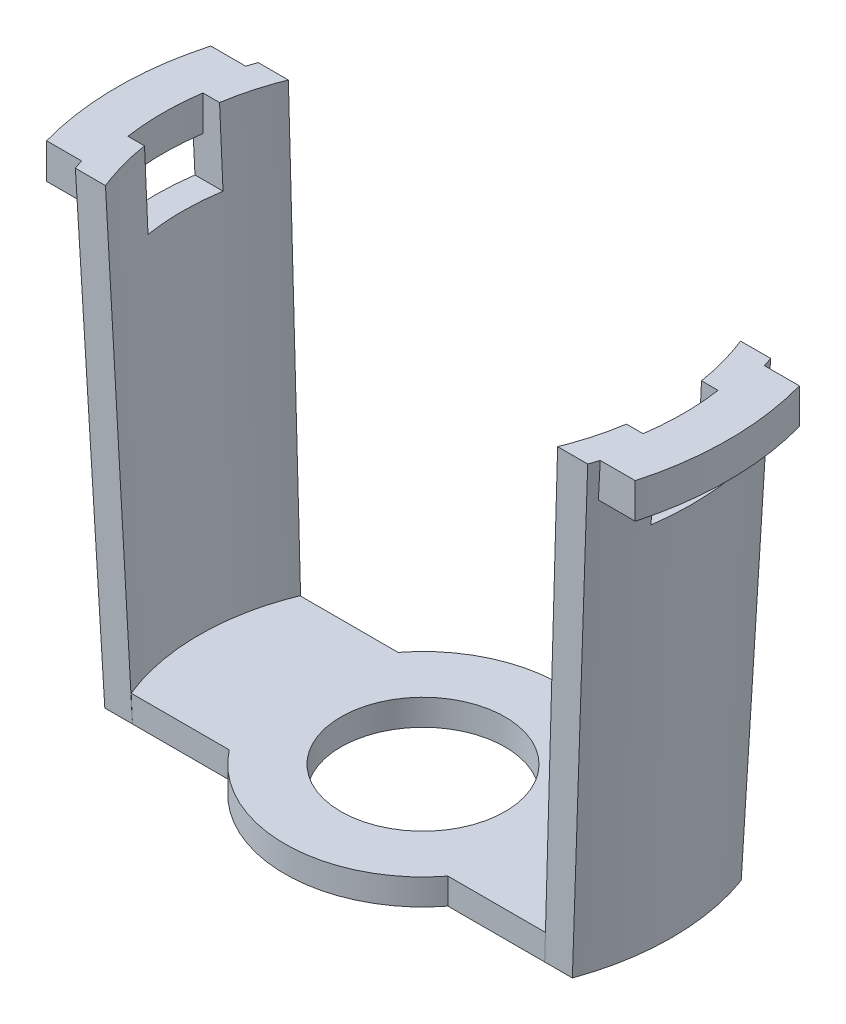
SolidWorks part; units mm, degrees
material "PE Low/Medium Density"
ref_plane "Front Plane" through (0, 0, 0) normal (0, 0, 1) x (1, 0, 0)
ref_plane "Top Plane" through (0, 0, 0) normal (0, 1, 0) x (1, 0, 0)
ref_plane "Right Plane" through (0, 0, 0) normal (1, 0, 0) x (0, 0, -1)
sketch "Sketch1" plane through (0, 0, 0) normal (0, 1, 0) x (1, 0, 0)
  line L0 (-13.462, 0) -> (13.462, 0) construction
  line L1 (-12.6618, 4.572) -> (-5.9204, 4.572)
  line L2 (5.9204, 4.572) -> (12.6618, 4.572)
  line L3 (-12.6618, -4.572) -> (-5.9204, -4.572)
  line L4 (5.9204, -4.572) -> (12.6618, -4.572)
  arc A0 (-5.9204, -4.572) -> (5.9204, -4.572) centre (0, 0) ccw
  circle A1 centre (0, 0) radius 4.445
  arc A2 (-12.6618, 4.572) -> (-12.6618, -4.572) centre (0, 0) ccw
  arc A3 (12.6618, -4.572) -> (12.6618, 4.572) centre (0, 0) ccw
  arc A4 (5.9204, 4.572) -> (-5.9204, 4.572) centre (0, 0) ccw
  dimension "D1" = 7.4803
  dimension "D2" = 8.89
  dimension "D4" = 13.462
  dimension "D5" = 9.144
extrude "Base" add sketch "Sketch1" along normal blind 1.4097
ref_plane "Plane1" through (0, 24.9047, 0) normal (0, -1, 0) x (-1, 0, 0)
sketch "Sketch3" plane through (0, 0, 0) normal (0, 1, 0) x (1, 0, 0)
  line L0 (-12.6618, -4.572) -> (-11.1632, -4.572)
  line L1 (-12.6618, -4.572) -> (-5.9204, -4.572) construction
  line L2 (-12.6618, 4.572) -> (-11.1632, 4.572)
  line L3 (-5.9204, 4.572) -> (-12.6618, 4.572) construction
  arc A0 (-12.6618, -4.572) -> (-12.6618, 4.572) centre (0, 0) cw
  arc A1 (-11.1632, 4.572) -> (-11.1632, -4.572) centre (0, 0) ccw
  arc A2 (-12.6618, 4.572) -> (-12.6618, -4.572) centre (0, 0) ccw construction
  dimension "D2" = 1.4986
sketch "Sketch2" plane through (0, 24.9047, 0) normal (0, -1, 0) x (-1, 0, 0)
  line L0 (12.2441, 4.953) -> (13.8744, 4.953)
  line L1 (16.2643, 0) -> (-1.4298, 0) construction
  line L2 (12.2441, -4.953) -> (13.8744, -4.953)
  arc A0 (13.8744, -4.953) -> (13.8744, 4.953) centre (0, 0) ccw
  arc A1 (12.2441, -4.953) -> (12.2441, 4.953) centre (0, 0) ccw
  dimension "D1" = 13.208
  dimension "D2" = 1.524
  dimension "D3" = 9.906
loft "Arm loft" add profiles "Sketch3", "Sketch2"
mirror "Mirror of arm loft" about plane through (0, 0, 0) normal (1, 0, 0) of "Arm loft"
sketch "Sketch4" plane through (0, 24.9047, 0) normal (0, -1, 0) x (-1, 0, 0)
  line L0 (12.4376, 4.445) -> (15.9399, 4.445)
  line L1 (12.4376, -4.445) -> (15.9399, -4.445)
  line L2 (12.2441, 4.953) -> (13.8744, 4.953) construction
  line L3 (12.2441, -4.953) -> (13.8744, -4.953) construction
  line L4 (13.208, 0) -> (16.5481, 0) construction
  line L5 (16.5481, 0) -> (0, 0) construction
  arc A0 (15.9399, -4.445) -> (15.9399, 4.445) centre (0, 0) ccw
  arc A1 (12.4376, 4.445) -> (12.4376, -4.445) centre (0, 0) cw
  arc A2 (12.2441, -4.953) -> (12.2441, 4.953) centre (0, 0) ccw construction
  dimension "D2" = 0.508
  dimension "D3" = 0.508
  dimension "D1" = 3.3401
extrude "Radial flange" add sketch "Sketch4" along normal blind 1.905
sketch "Sketch5" plane through (0, 24.9047, 0) normal (0, 1, 0) x (1, 0, 0)
  line L0 (0, 0) -> (-16.5481, 0) construction
  line L1 (-11.2479, 2.032) -> (-13.9498, 2.032)
  line L2 (-11.2479, -2.032) -> (-13.9498, -2.032)
  arc A0 (-15.9399, 4.445) -> (-15.9399, -4.445) centre (0, 0) ccw construction
  arc A1 (-11.2479, 2.032) -> (-11.2479, -2.032) centre (0, 0) ccw
  arc A3 (-13.9498, 2.032) -> (-13.9498, -2.032) centre (0, 0) ccw
  dimension "D1" = 14.097
  dimension "D4" = 11.43
  dimension "D2" = 2.032
  dimension "D3" = 2.032
extrude "Axial cut-out" cut sketch "Sketch5" against normal blind 4.064
mirror "Mirror of radial flange and axial cut-out" about plane through (0, 0, 0) normal (1, 0, 0) of "Radial flange", "Axial cut-out"
sketch "Sketch6" plane through (0, 0, 0) normal (1, 0, 0) x (0, 0, -1)
  line L0 (2.032, 20.8407) -> (2.032, 22.9997)
  line L2 (-2.032, 20.8407) -> (-2.032, 22.9997)
  line L3 (-2.032, 22.9997) -> (2.032, 22.9997)
  line L4 (2.032, 20.8407) -> (-2.032, 20.8407)
  line L5 (-4.445, 22.9997) -> (4.445, 22.9997) construction
  line L6 (-4.445, 22.9997) -> (4.445, 22.9997) construction
extrude "Radial cut-out" cut sketch "Sketch6" against normal through all both and the other way through all
equation "\"D2@Sketch4\"=\"D3@Sketch4\""
equation "\"D2@Sketch5\"=\"D3@Sketch5\""
